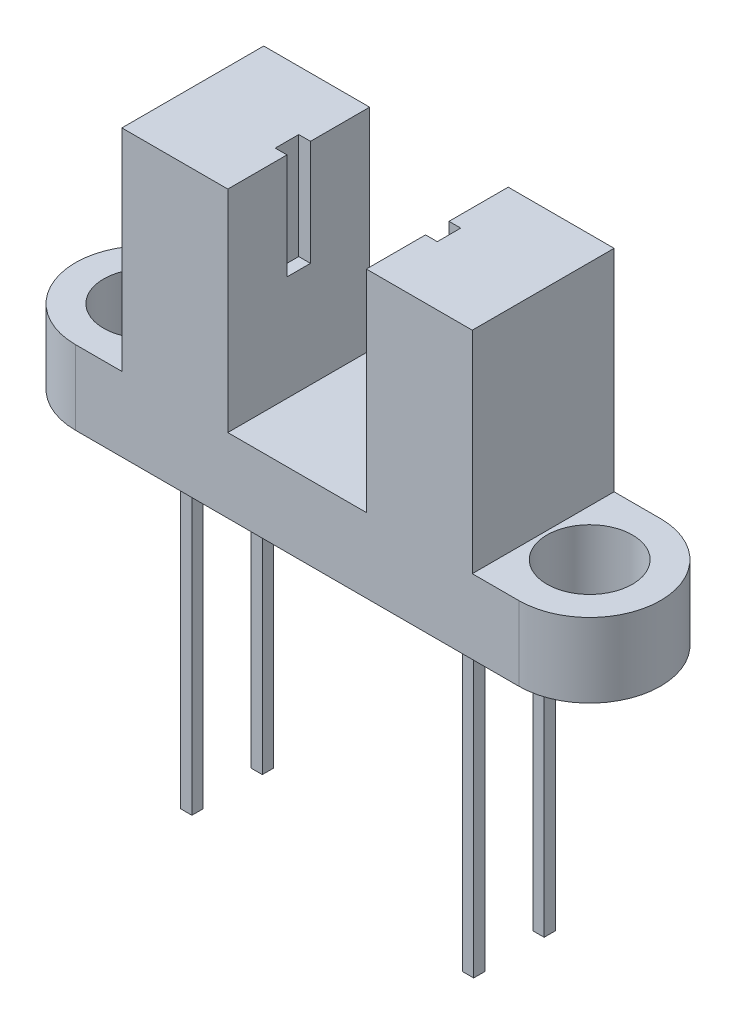
SolidWorks part; units mm, degrees
ref_plane "Alzado" through (0, 0, 0) normal (0, 0, 1) x (1, 0, 0)
ref_plane "Planta" through (0, 0, 0) normal (0, 1, 0) x (1, 0, 0)
ref_plane "Vista lateral" through (0, 0, 0) normal (1, 0, 0) x (0, 0, -1)
sketch "Croquis1" plane through (0, 0, 0) normal (0, 1, 0) x (1, 0, 0)
  line L0 (-9.44, 0) -> (9.44, 0) construction
  line L1 (-9.44, 3.02) -> (9.44, 3.02)
  line L2 (-9.44, -3.02) -> (9.44, -3.02)
  arc A0 (-9.44, 3.02) -> (-9.44, -3.02) centre (-9.44, 0) ccw
  arc A1 (9.44, -3.02) -> (9.44, 3.02) centre (9.44, 0) ccw
  circle A2 centre (-9.44, 0) radius 1.82
  circle A3 centre (9.44, 0) radius 1.82
  point P3 (0, 0)
  dimension "D2" = 18.88
  dimension "D3" = 3.64
  dimension "D4" = 3.64
  dimension "D1" = 6.04
extrude "Saliente-Extruir1" add sketch "Croquis1" along normal blind 3.16
sketch "Croquis2" plane through (0, 3.16, 0) normal (0, 1, 0) x (1, 0, 0)
  line L0 (0, 0) -> (0, 3.02) construction
  line L1 (9.44, 3.02) -> (-9.44, 3.02) construction
  line L2 (-9.44, -3.02) -> (9.44, -3.02) construction
  line L3 (2.95, -3.02) -> (7.46, -3.02)
  line L4 (2.95, -3.02) -> (2.95, 3.02)
  line L5 (2.95, 3.02) -> (7.46, 3.02)
  line L6 (7.46, -3.02) -> (7.46, 3.02)
  line L8 (-7.46, 3.02) -> (-2.95, 3.02)
  line L9 (-7.46, 3.02) -> (-7.46, -3.02)
  line L10 (-7.46, -3.02) -> (-2.95, -3.02)
  line L11 (-2.95, 3.02) -> (-2.95, -3.02)
  dimension "D1" = 14.92
  dimension "D2" = 7.46
  dimension "D3" = 5.9
  dimension "D4" = 2.95
extrude "Saliente-Extruir2" add sketch "Croquis2" along normal blind 8.98
sketch "Croquis3" plane through (0, 0, 0) normal (0, -1, 0) x (1, 0, 0)
  line L0 (5.76, 1.74) -> (6.24, 1.74)
  line L1 (-6, -1.5) -> (6, -1.5) construction
  line L2 (-6, -1.5) -> (-6, 1.5) construction
  line L3 (-6, 1.5) -> (6, 1.5) construction
  line L4 (6, -1.5) -> (6, 1.5) construction
  line L5 (-6, -1.5) -> (6, 1.5) construction
  line L6 (-6, 1.5) -> (6, -1.5) construction
  line L7 (-6.24, 1.26) -> (-5.76, 1.26)
  line L8 (-6.24, 1.26) -> (-6.24, 1.74)
  line L9 (-6.24, 1.74) -> (-5.76, 1.74)
  line L10 (-5.76, 1.26) -> (-5.76, 1.74)
  line L11 (-6.24, 1.26) -> (-5.76, 1.74) construction
  line L12 (-6.24, 1.74) -> (-5.76, 1.26) construction
  line L13 (5.76, 1.74) -> (6.24, 1.26) construction
  line L14 (5.76, 1.26) -> (5.76, 1.74)
  line L15 (6.24, 1.26) -> (6.24, 1.74)
  line L16 (5.76, 1.26) -> (6.24, 1.26)
  line L17 (5.76, 1.26) -> (6.24, 1.74) construction
  line L18 (5.76, -1.26) -> (6.24, -1.26)
  line L19 (5.76, -1.26) -> (6.24, -1.74) construction
  line L20 (5.76, -1.74) -> (5.76, -1.26)
  line L21 (6.24, -1.74) -> (6.24, -1.26)
  line L22 (5.76, -1.74) -> (6.24, -1.74)
  line L23 (5.76, -1.74) -> (6.24, -1.26) construction
  line L24 (-6.24, -1.26) -> (-5.76, -1.26)
  line L25 (-6.24, -1.26) -> (-5.76, -1.74) construction
  line L26 (-6.24, -1.74) -> (-6.24, -1.26)
  line L27 (-5.76, -1.74) -> (-5.76, -1.26)
  line L28 (-6.24, -1.74) -> (-5.76, -1.74)
  line L29 (-6.24, -1.74) -> (-5.76, -1.26) construction
  point P0 (0, 0)
  dimension "D1" = 12
  dimension "D2" = 3
  dimension "D3" = 0.48
  dimension "D4" = 0.48
  dimension "D5" = 2
  dimension "D6" = 2
extrude "Saliente-Extruir3" add sketch "Croquis3" along normal blind 13 separate body
sketch "Croquis4" plane through (0, 12.14, 0) normal (0, 1, 0) x (1, 0, 0)
  line L0 (2.95, 3.02) -> (2.95, -3.02) construction
  line L1 (-3.45, 0.5) -> (3.45, 0.5)
  line L2 (-3.45, 0.5) -> (-3.45, -0.5)
  line L3 (-3.45, -0.5) -> (3.45, -0.5)
  line L4 (3.45, 0.5) -> (3.45, -0.5)
  line L5 (-3.45, 0.5) -> (3.45, -0.5) construction
  line L6 (-3.45, -0.5) -> (3.45, 0.5) construction
  point P0 (0, 0)
  dimension "D1" = 0.5
  dimension "D2" = 1
extrude "Cortar-Extruir1" cut sketch "Croquis4" against normal blind 4.5
